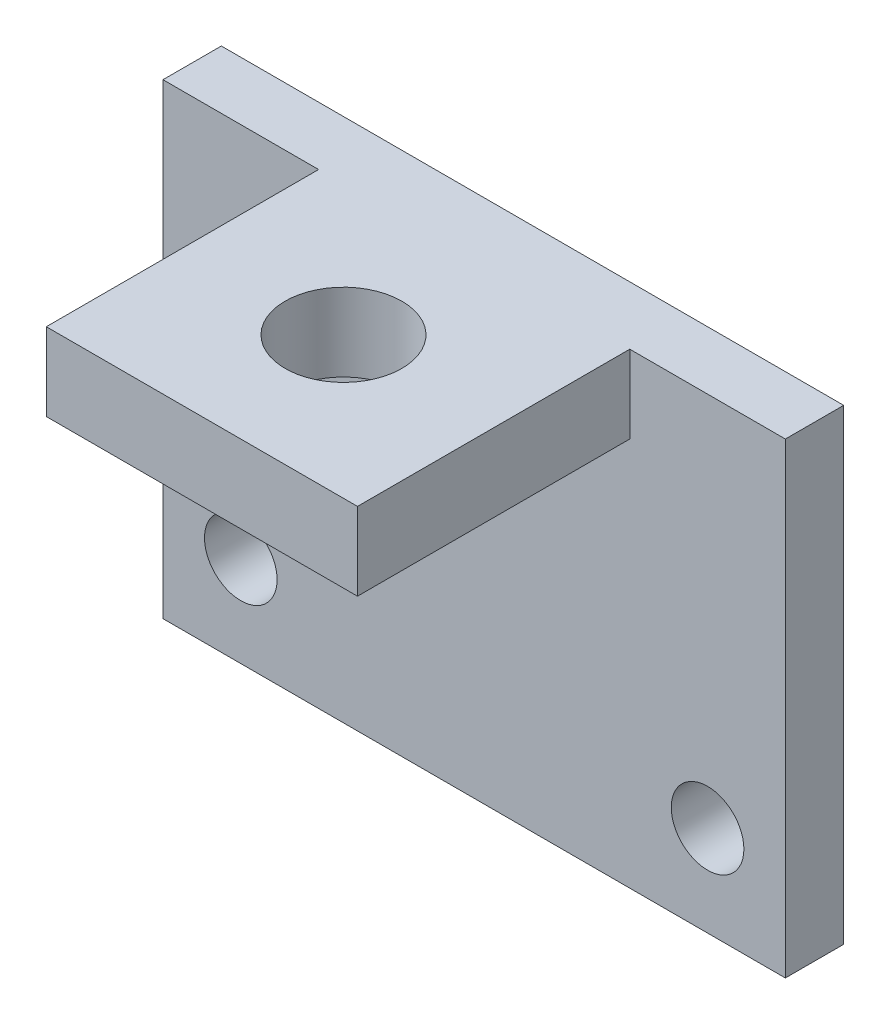
SolidWorks part; units mm, degrees
ref_plane "Front" through (0, 0, 0) normal (0, 0, 1) x (1, 0, 0)
ref_plane "Top" through (0, 0, 0) normal (0, 1, 0) x (1, 0, 0)
ref_plane "Right" through (0, 0, 0) normal (1, 0, 0) x (0, 0, -1)
sketch "草图2" plane through (0, 0, 0) normal (0, 0, 1) x (1, 0, 0)
  line L1 (0, 0) -> (16, 0)
  line L2 (0, 0) -> (0, 12)
  line L3 (0, 12) -> (16, 12)
  line L4 (16, 0) -> (16, 12)
  circle A0 centre (2, 2.3341) radius 0.9336
  circle A1 centre (14, 2.3341) radius 0.9336
  dimension "D1" = 2
  dimension "D2" = 2
extrude "凸台-拉伸1" add sketch "草图2" along normal blind 1.5
sketch "草图3" plane through (0, 0, 1.5) normal (0, 0, 1) x (1, 0, 0)
  line L5 (16, 12) -> (0, 12) construction
  line L6 (4, 12) -> (12, 12)
  line L7 (4, 12) -> (4, 10)
  line L8 (4, 10) -> (12, 10)
  line L9 (12, 12) -> (12, 10)
  line L10 (0, 12) -> (0, 0) construction
  line L11 (16, 0) -> (16, 12) construction
  dimension "D1" = 4
  dimension "D2" = 4
extrude "凸台-拉伸2" add sketch "草图3" along normal blind 7
sketch "草图4" plane through (0, 10, 0) normal (0, -1, 0) x (1, 0, 0)
  line L0 (4, 1.5) -> (12, 1.5) construction
  circle A0 centre (8, 4.86) radius 1.5
  dimension "D1" = 3.36
extrude "切除-拉伸1" cut sketch "草图4" against normal blind 3 contours A0
